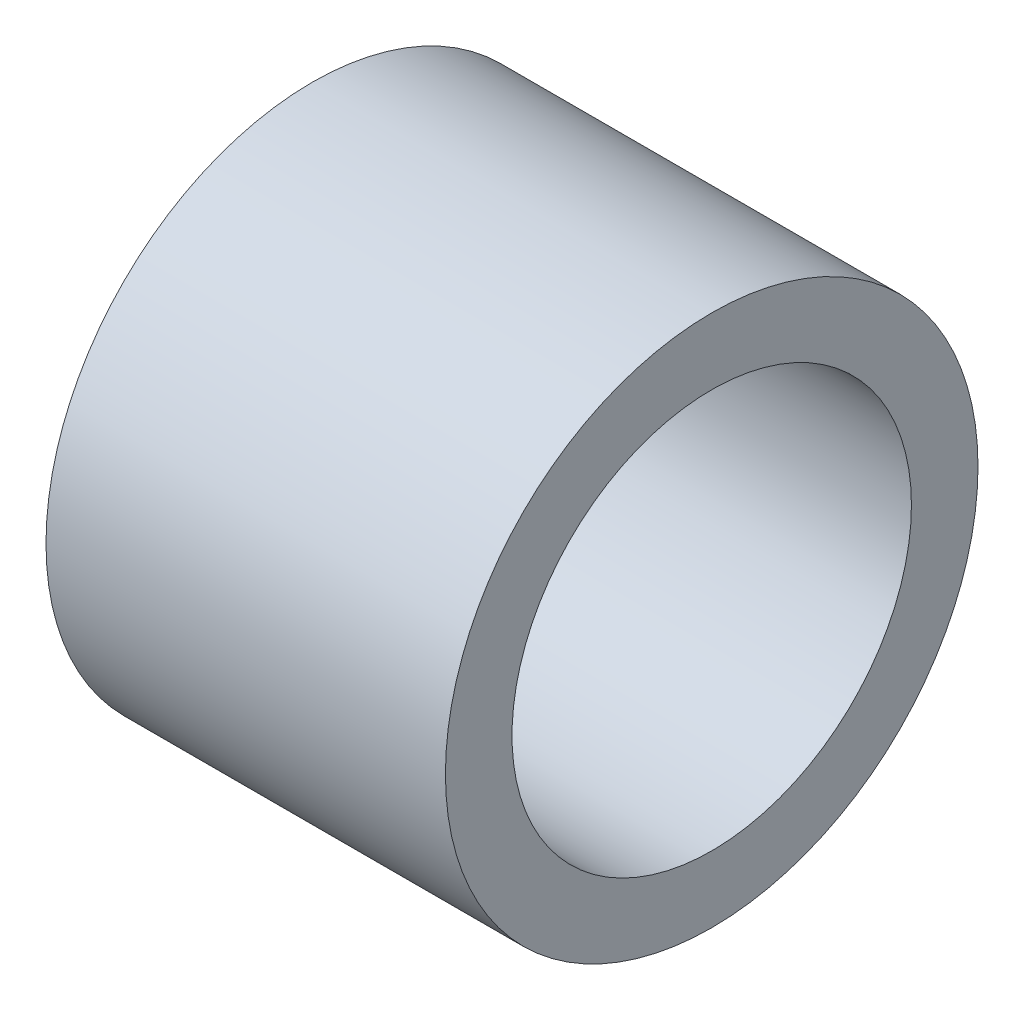
SolidWorks part; units mm, degrees
ref_plane "Front Plane" through (0, 0, 0) normal (0, 0, 1) x (1, 0, 0)
ref_plane "Top Plane" through (0, 0, 0) normal (0, 1, 0) x (1, 0, 0)
ref_plane "Right Plane" through (0, 0, 0) normal (1, 0, 0) x (0, 0, -1)
sketch "Sketch2" plane through (0, 0, 0) normal (1, 0, 0) x (0, 0, -1)
  circle A0 centre (0, 0) radius 9.525
  circle A1 centre (0, 0) radius 12.7
  dimension "D1" = 19.05
  dimension "D2" = 25.4
extrude "Boss-Extrude1" add sketch "Sketch2" along normal mid plane 19.05
